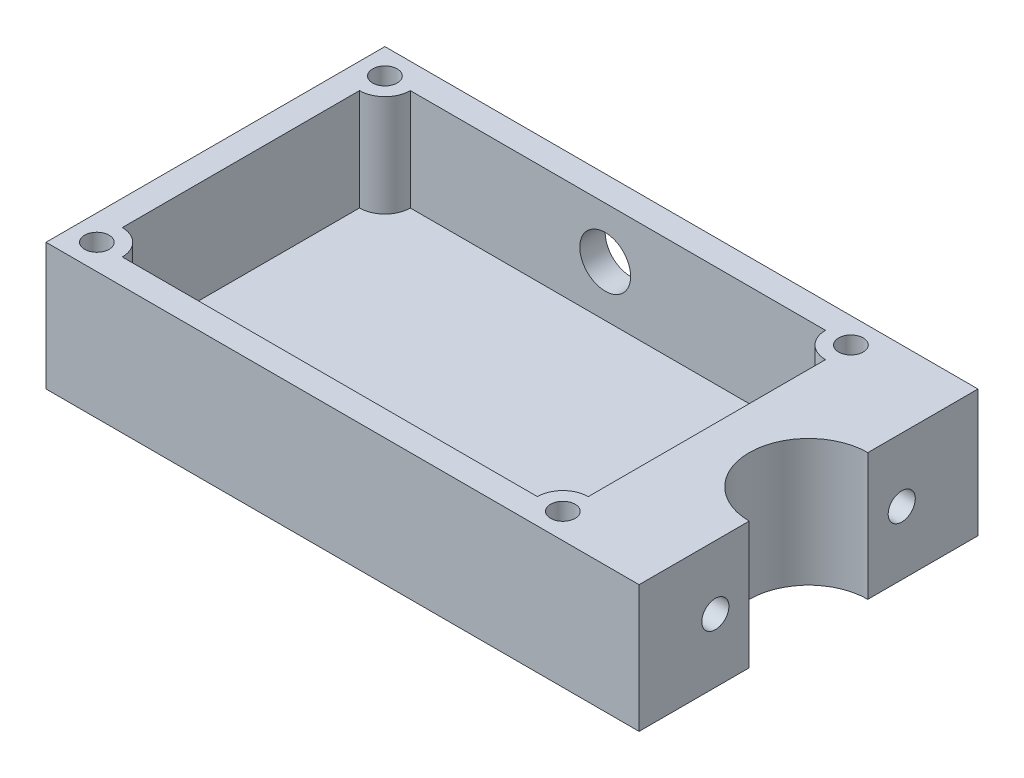
SolidWorks part; units mm, degrees
ref_plane "Спереди" through (0, 0, 0) normal (0, 0, 1) x (1, 0, 0)
ref_plane "Сверху" through (0, 0, 0) normal (0, 1, 0) x (1, 0, 0)
ref_plane "Справа" through (0, 0, 0) normal (1, 0, 0) x (0, 0, -1)
sketch "Sketch1" plane through (0, 0, 0) normal (0, 1, 0) x (1, 0, 0)
  line L0 (35, 20) -> (35, 7)
  line L1 (35, -20) -> (-35, -20)
  line L2 (35, -20) -> (35, 20) construction
  line L3 (35, 20) -> (-35, 20)
  line L4 (-35, -20) -> (-35, 20)
  line L5 (35, -20) -> (-35, 20) construction
  line L6 (35, 20) -> (-35, -20) construction
  line L7 (35, -7) -> (35, -20)
  arc A0 (35, 7) -> (35, -7) centre (35, 0) ccw
  point P0 (0, 0)
  dimension "D3" = 7
  dimension "D1" = 70
  dimension "D2" = 40
extrude "Boss-Extrude1" add sketch "Sketch1" along normal blind 15
sketch "Sketch2" plane through (0, 15, 0) normal (0, 1, 0) x (1, 0, 0)
  line L0 (-30.2502, 0) -> (28, 0) construction
  line L1 (-35, 20) -> (-35, -20) construction
  line L2 (23, -17) -> (-32, -17)
  line L3 (23, -17) -> (23, 17)
  line L4 (23, 17) -> (-32, 17)
  line L5 (-32, -17) -> (-32, 17)
  line L6 (23, -17) -> (-32, 17) construction
  line L7 (23, 17) -> (-32, -17) construction
  line L8 (35, 20) -> (-35, 20) construction
  arc A0 (35, 7) -> (35, -7) centre (35, 0) ccw construction
  point P5 (-4.5, 0)
  dimension "D1" = 3
  dimension "D2" = 3
  dimension "D3" = 55
extrude "Cut-Extrude1" cut sketch "Sketch2" against normal offset from surface (12 mm away) 3 up to face at (10.5, 0, 0)
sketch "Sketch4" plane through (35, 0, 0) normal (1, 0, 0) x (0, 0, -1)
  line L0 (20, 7.5) -> (-20, 7.5) construction
  line L1 (20, 15) -> (20, 0) construction
  line L2 (-20, 15) -> (-20, 0) construction
  circle A0 centre (11, 7.5) radius 1.6
  circle A1 centre (-11, 7.5) radius 1.6
  point P10 (0, 7.5)
  dimension "D1" = 22
  dimension "D3" = 3.2
  dimension "D2" = 11
extrude "Cut-Extrude2" cut sketch "Sketch4" against normal up to next
sketch "Sketch5" plane through (23, 0, 0) normal (-1, 0, 0) x (0, 0, 1)
  line L0 (17, 3) -> (17, 15) construction
  line L1 (-11, 10.75) -> (-13.8146, 9.125)
  line L2 (-13.8146, 9.125) -> (-13.8146, 5.875)
  line L3 (-13.8146, 5.875) -> (-11, 4.25)
  line L4 (-11, 4.25) -> (-8.1854, 5.875)
  line L5 (-8.1854, 5.875) -> (-8.1854, 9.125)
  line L6 (-8.1854, 9.125) -> (-11, 10.75)
  line L7 (8.1854, 9.125) -> (8.1854, 5.875)
  line L8 (8.1854, 5.875) -> (11, 4.25)
  line L9 (11, 4.25) -> (13.8146, 5.875)
  line L10 (13.8146, 5.875) -> (13.8146, 9.125)
  line L11 (13.8146, 9.125) -> (11, 10.75)
  line L12 (11, 10.75) -> (8.1854, 9.125)
  circle A0 centre (-11, 7.5) radius 3.25 construction
  circle A1 centre (11, 7.5) radius 3.25 construction
  dimension "D1" = 6.5
extrude "Cut-Extrude3" cut sketch "Sketch5" against normal blind 4
sketch "Sketch6" plane through (0, 15, 0) normal (0, 1, 0) x (1, 0, 0)
  line L0 (23, 17) -> (-32, 17) construction
  line L1 (-32, 17) -> (-32, -17) construction
  line L2 (-32, -17) -> (23, -17) construction
  line L3 (23, -17) -> (23, 17) construction
  line L4 (-32, -14) -> (-32, -17)
  line L5 (-32, -17) -> (-29, -17)
  line L6 (23, -14) -> (23, -17)
  line L7 (23, -17) -> (20, -17)
  line L8 (20, 17) -> (23, 17)
  line L9 (23, 17) -> (23, 14)
  line L10 (-32, 14) -> (-32, 17)
  line L12 (-32, 17) -> (-29, 17)
  arc A0 (-29, 17) -> (-32, 14) centre (-32, 17) cw
  arc A1 (-32, -14) -> (-29, -17) centre (-32, -17) cw
  arc A2 (20, -17) -> (23, -14) centre (23, -17) cw
  arc A3 (23, 14) -> (20, 17) centre (23, 17) cw
  point P24 (-32, 14)
  dimension "D1" = 3
extrude "Boss-Extrude3" add sketch "Sketch6" against normal up to next
sketch "Sketch7" plane through (0, 15, 0) normal (0, 1, 0) x (1, 0, 0)
  circle A0 centre (-32, 17) radius 1.45
  circle A1 centre (23, 17) radius 1.45
  circle A2 centre (23, -17) radius 1.45
  circle A3 centre (-32, -17) radius 1.45
  dimension "D1" = 2.9
extrude "Cut-Extrude4" cut sketch "Sketch7" against normal through all
sketch "Sketch8" plane through (0, 0, -17) normal (0, 0, 1) x (1, 0, 0)
  line L0 (-29, 3) -> (20, 3) construction
  line L3 (-29, 9) -> (17, 9) construction
  line L4 (-29, 9) -> (-29, 15) construction
  line L5 (20, 15) -> (-29, 15) construction
  circle A0 centre (-6, 9) radius 3
  point P0 (-4.6795, 9)
  point P1 (-6, 9)
  dimension "D1" = 6
  dimension "D2" = 6
  dimension "D3" = 46
  dimension "D4" = 6
extrude "Cut-Extrude5" cut sketch "Sketch8" against normal through all
